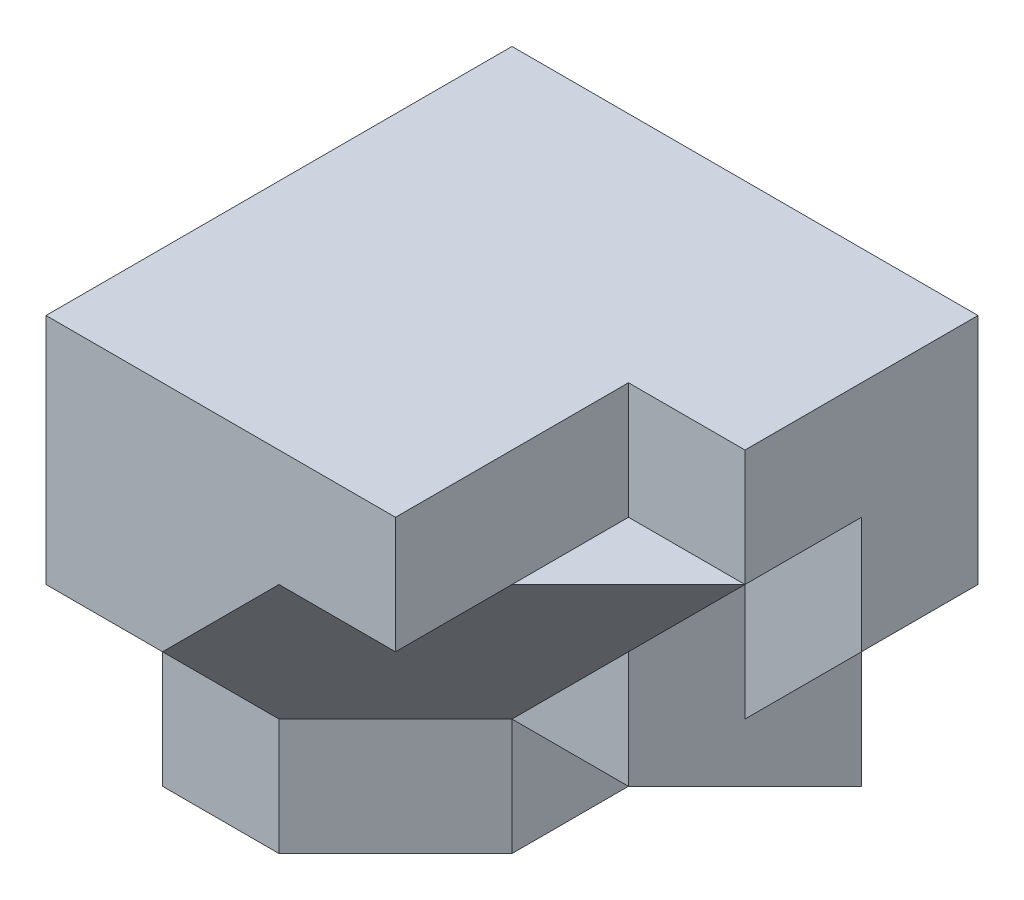
SolidWorks part; units mm, degrees
ref_plane "Front Plane" through (0, 0, 0) normal (0, 0, 1) x (1, 0, 0)
ref_plane "Top Plane" through (0, 0, 0) normal (0, 1, 0) x (1, 0, 0)
ref_plane "Right Plane" through (0, 0, 0) normal (1, 0, 0) x (0, 0, -1)
sketch "Sketch1" plane through (0, 0, 0) normal (0, 0, 1) x (1, 0, 0)
  line L1 (0, 0) -> (40, 0)
  line L2 (0, 0) -> (0, 40)
  line L3 (0, 40) -> (40, 40)
  line L4 (40, 0) -> (40, 40)
  dimension "D1" = 40
  dimension "D2" = 40
extrude "Boss-Extrude1" add sketch "Sketch1" along normal blind 20
sketch "Sketch2" plane through (0, 0, 20) normal (0, 0, 1) x (1, 0, 0)
  line L0 (20, 0) -> (20, 10)
  line L1 (0, 0) -> (40, 0) construction
  line L2 (20, 10) -> (40, 30)
  line L3 (40, 0) -> (40, 40) construction
  line L4 (40, 30) -> (40, 40)
  line L5 (40, 30) -> (40, 0)
  line L6 (40, 0) -> (20, 0)
  line M2 (0, 0) -> (40, 0)
  line M3 (40, 0) -> (40, 40)
  dimension "D1" = 10
  dimension "D2" = 20
  dimension "D3" = 20
extrude "Cut-Extrude1" cut sketch "Sketch2" against normal blind 20 contours L2 L0 M2 M3
sketch "Sketch3" plane through (0, 0, 0) normal (0, -1, 0) x (1, 0, 0)
  line L0 (20, 20) -> (0, 20)
  line L1 (0, 20) -> (0, 30)
  line L2 (0, 30) -> (10, 30)
  line L3 (10, 30) -> (20, 20)
  dimension "D1" = 10
  dimension "D2" = 10
extrude "Boss-Extrude2" add sketch "Sketch3" against normal blind 10
sketch "Sketch4" plane through (20, 0, 0) normal (1, 0, 0) x (0, 0, -1)
  line L0 (0, 0) -> (-20, 10)
  line L1 (-20, 10) -> (0, 10)
  line L2 (0, 10) -> (0, 0)
extrude "Boss-Extrude3" add sketch "Sketch4" along normal blind 10
sketch "Sketch5" plane through (0, 0, 20) normal (0, 0, 1) x (1, 0, 0)
  line L1 (20, 10) -> (30, 10)
  line L2 (20, 10) -> (20, 22.4776)
  line L3 (20, 22.4776) -> (30, 22.4776)
  line L4 (30, 10) -> (30, 22.4776)
  dimension "D1" = 10
extrude "Boss-Extrude4" add sketch "Sketch5" against normal blind 20
sketch "Sketch6" plane through (0, 0, 0) normal (0, 0, -1) x (-1, 0, 0)
  line L0 (-30, 10) -> (-40, 20)
  line L1 (-30, 0) -> (-30, 20) construction
  line L2 (-40, 20) -> (-40, 30)
  line L3 (-30, 10) -> (-30, 20)
  line L4 (-30, 20) -> (-40, 30)
  dimension "D1" = 10
  dimension "D2" = 10
  dimension "D3" = 10
extrude "Boss-Extrude5" add sketch "Sketch6" against normal blind 10
sketch "Sketch7" plane through (0, 0, 20) normal (0, 0, 1) x (1, 0, 0)
  line L1 (0, 40) -> (30, 40)
  line L2 (0, 40) -> (0, 30)
  line L3 (0, 30) -> (30, 30)
  line L4 (30, 40) -> (30, 30)
  dimension "D1" = 30
  dimension "D2" = 10
extrude "Boss-Extrude6" add sketch "Sketch7" along normal blind 20
sketch "Sketch8" plane through (0, 0, 0) normal (-1, 0, 0) x (0, 0, 1)
  line L0 (40, 30) -> (40, 20)
  line L1 (40, 20) -> (30, 10)
  line L2 (30, 10) -> (20, 10)
  line L3 (20, 10) -> (20, 30)
  line L4 (20, 30) -> (40, 30)
  dimension "D1" = 10
extrude "Boss-Extrude7" add sketch "Sketch8" against normal blind 10
sketch "Sketch9" plane through (0, 0, 40) normal (0, 0, 1) x (1, 0, 0)
  line L0 (10, 20) -> (20, 30)
  line L1 (10, 30) -> (30, 30) construction
  line L2 (20, 30) -> (10, 30)
  line L3 (10, 30) -> (10, 20)
  dimension "D1" = 10
extrude "Boss-Extrude8" add sketch "Sketch9" against normal blind 20
sketch "Sketch10" plane through (0, 30, 0) normal (0, -1, 0) x (-1, 0, 0)
  line L0 (-20, -40) -> (-40, -20)
sketch "Sketch11" plane through (0, 0, 20) normal (0, 0, 1) x (1, 0, 0)
  line L0 (40, 30) -> (20, 10)
ref_plane "Plane1" through (10, -10, 10) normal (-0.5774, 0.5774, -0.5774) x (-0.8165, -0.4082, 0.4082)
sketch "Sketch12" plane through (10, -10, 10) normal (-0.5774, 0.5774, -0.5774) x (-0.8165, -0.4082, 0.4082)
  line L0 (0, 42.4264) -> (-12.2474, 49.4975)
  line L1 (-12.2474, 49.4975) -> (-36.7423, 35.3553)
  line L2 (-36.7423, 35.3553) -> (-12.2474, 21.2132)
  line L3 (-12.2474, 21.2132) -> (0, 28.2843)
  line L4 (0, 28.2843) -> (0, 42.4264)
  line L5 (0, 42.4264) -> (-12.2474, 21.2132)
  line L6 (-12.2474, 49.4975) -> (-24.4949, 28.2843)
sketch "Sketch13" plane through (0, 40, 0) normal (0, 1, 0) x (1, 0, 0)
  line L1 (30, -20) -> (40, -20)
  line L2 (30, -20) -> (30, -30)
  line L3 (30, -30) -> (40, -30)
  line L4 (40, -20) -> (40, -30)
  dimension "D1" = 10
  dimension "D2" = 10
extrude "Boss-Extrude10" add sketch "Sketch13" against normal blind 10
extrude "Boss-Extrude13" add sketch "Sketch12" along normal blind 10 contours L0 L6 L2 L5
sketch "Sketch14" plane through (10, -10, 10) normal (-0.5774, 0.5774, -0.5774) x (-0.8165, -0.4082, 0.4082)
  line L0 (0, 42.4264) -> (0, 28.2843)
  line L1 (0, 28.2843) -> (-12.2474, 21.2132)
  line L2 (-12.2474, 21.2132) -> (0, 42.4264)
sketch "Sketch15" plane through (0, 40, 0) normal (0, 1, 0) x (1, 0, 0)
  line L0 (0, -40) -> (0, 0) construction
  line L1 (0, -9.6197) -> (20, -9.6197)
  line L2 (0, -9.6197) -> (0, -40)
  line L3 (0, -40) -> (20, -40)
  line L4 (20, -9.6197) -> (20, -40)
  line L5 (30, -40) -> (0, -40) construction
  dimension "D1" = 20
extrude "Boss-Extrude15" add sketch "Sketch15" against normal blind 30
sketch "Sketch17" plane through (10, -10, 10) normal (-0.5774, 0.5774, -0.5774) x (-0.8165, -0.4082, 0.4082)
  line L0 (-12.2474, 49.4975) -> (0, 42.4264)
  line L1 (0, 42.4264) -> (-12.2474, 21.2132)
  line L2 (-12.2474, 21.2132) -> (-12.2474, 49.4975)
extrude "Cut-Extrude2" cut sketch "Sketch17" against normal blind 30
sketch "Sketch18" plane through (10, -10, 10) normal (-0.5774, 0.5774, -0.5774) x (-0.8165, -0.4082, 0.4082)
  line L0 (0, 42.4264) -> (0, 28.2843)
  line L1 (0, 28.2843) -> (-12.2474, 21.2132)
  line L2 (-12.2474, 21.2132) -> (0, 42.4264)
extrude "Cut-Extrude3" cut sketch "Sketch18" against normal blind 30
sketch "Sketch20" plane through (0, 0, 0) normal (0.8165, 0.4082, -0.4082) x (-0.3651, -0.1826, -0.9129)
  line L0 (-32.8634, 4.4721) -> (-43.8178, 2.2361)
  line L1 (-43.8178, 2.2361) -> (-43.8178, 13.4164)
  line L2 (-43.8178, 13.4164) -> (-32.8634, 4.4721)
extrude "Cut-Extrude4" cut sketch "Sketch20" against normal blind 30
sketch "Sketch21" plane through (0, 0, 0) normal (-1, 0, 0) x (0, 0, 1)
  line L0 (30, 10) -> (40, 20)
  line L1 (40, 20) -> (40, 10)
  line L2 (40, 10) -> (30, 10)
  dimension "D1" = 10
  dimension "D2" = 10
extrude "Cut-Extrude5" cut sketch "Sketch21" against normal blind 30
sketch "Sketch23" plane through (10, -10, 10) normal (-0.5774, 0.5774, -0.5774) x (-0.8165, -0.4082, 0.4082)
  line L0 (-12.2474, 49.4975) -> (-24.4949, 28.2843)
  line L1 (-24.4949, 28.2843) -> (-36.7423, 35.3553)
  line L2 (-36.7423, 35.3553) -> (-12.2474, 49.4975)
extrude "Boss-Extrude16" add sketch "Sketch23" along normal blind 10
sketch "Sketch24" plane through (0, 40, 0) normal (0, 1, 0) x (1, 0, 0)
  line L0 (30, -30) -> (40, -20)
  line L1 (40, -30) -> (40, 0) construction
  line L2 (40, -20) -> (40, -30)
  line L3 (30, -30) -> (40, -30) construction
  line L4 (40, -30) -> (30, -30)
  dimension "D1" = 10
extrude "Cut-Extrude6" cut sketch "Sketch24" against normal blind 10
sketch "Sketch25" plane through (0, 40, 0) normal (0, 1, 0) x (1, 0, 0)
  line L0 (40, -20) -> (40, 0) construction
  line L1 (30, -30) -> (40, -30)
  line L2 (30, -30) -> (30, -20)
  line L3 (30, -20) -> (40, -20)
  line L4 (40, -30) -> (40, -20)
  line L5 (40, 0) -> (0, 0) construction
  dimension "D1" = 20
extrude "Cut-Extrude7" cut sketch "Sketch25" against normal blind 10
